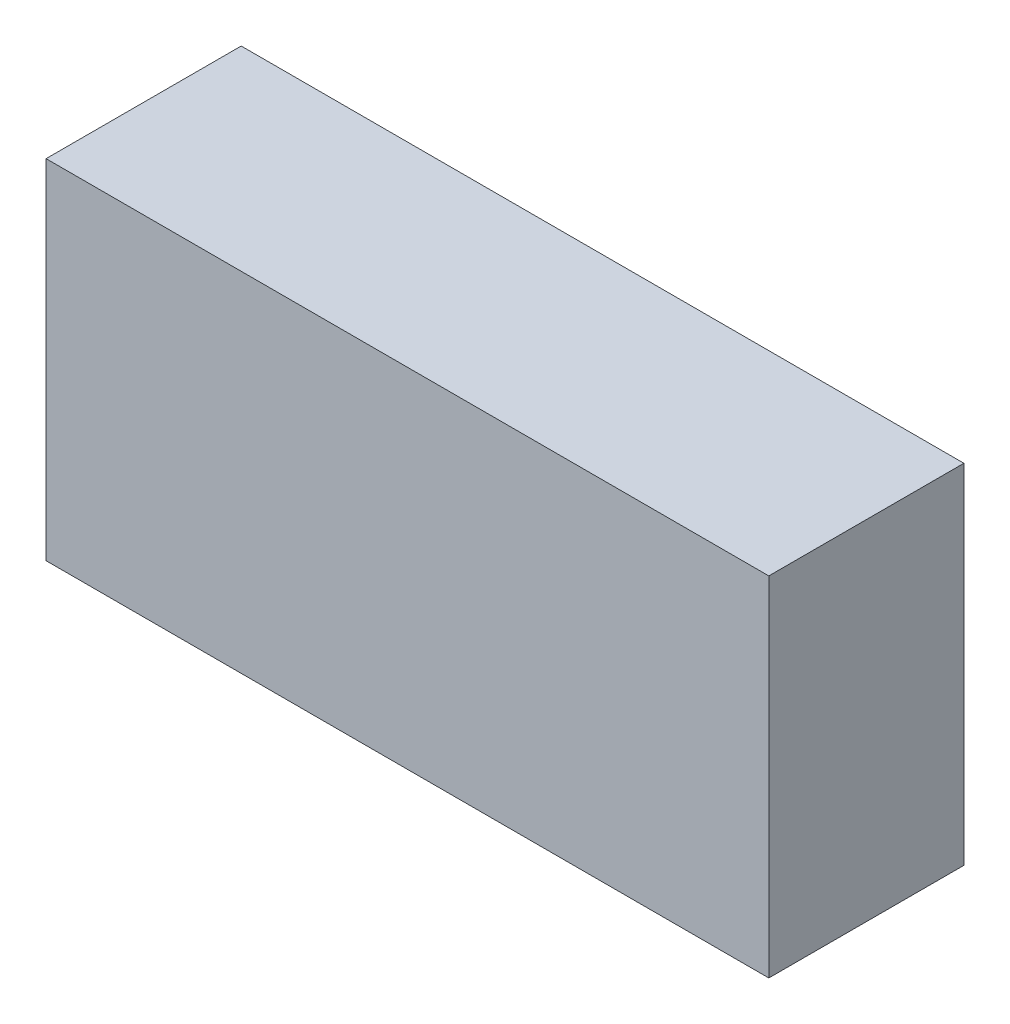
SolidWorks part; units mm, degrees
ref_plane "Front Plane" through (0, 0, 0) normal (0, 0, 1) x (1, 0, 0)
ref_plane "Top Plane" through (0, 0, 0) normal (0, 1, 0) x (1, 0, 0)
ref_plane "Right Plane" through (0, 0, 0) normal (1, 0, 0) x (0, 0, -1)
sketch "Sketch1" plane through (0, 0, 0) normal (0, 0, 1) x (1, 0, 0)
  line L1 (0, 0) -> (202, 0)
  line L2 (0, 0) -> (0, 97.33)
  line L3 (0, 97.33) -> (202, 97.33)
  line L4 (202, 0) -> (202, 97.33)
  dimension "D1" = 202
  dimension "D2" = 97.33
extrude "Boss-Extrude1" add sketch "Sketch1" along normal blind 54.53
